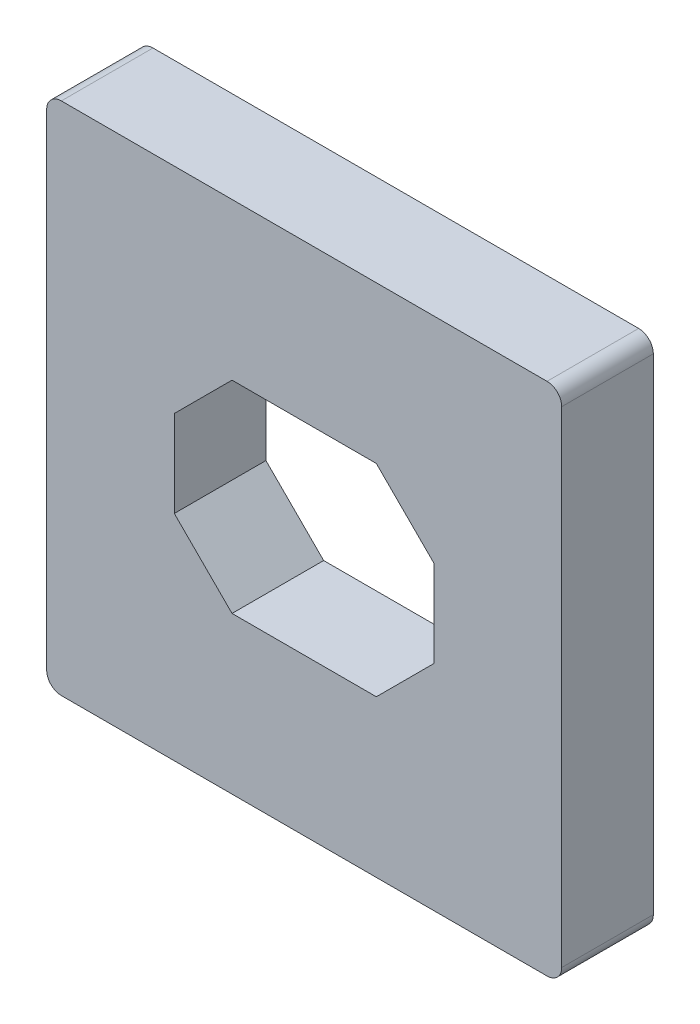
SolidWorks part; units mm, degrees
material "PET"
ref_plane "Front Plane" through (0, 0, 0) normal (0, 0, 1) x (1, 0, 0)
ref_plane "Top Plane" through (0, 0, 0) normal (0, 1, 0) x (1, 0, 0)
ref_plane "Right Plane" through (0, 0, 0) normal (1, 0, 0) x (0, 0, -1)
sketch "Sketch1" plane through (0, 0, 0) normal (0, 0, 1) x (1, 0, 0)
  line L0 (4.207, 4.715) -> (-4.207, 4.715) construction
  line L1 (4.715, -4.207) -> (4.715, 4.207) construction
  line L2 (-4.207, -4.715) -> (4.207, -4.715) construction
  line L3 (-4.715, 4.207) -> (-4.715, -4.207) construction
  line L4 (4.207, 4.715) -> (-4.207, 4.715) construction
  line L5 (4.715, -4.207) -> (4.715, 4.207) construction
  line L6 (-4.207, -4.715) -> (4.207, -4.715) construction
  line L7 (-4.715, 4.207) -> (-4.715, -4.207) construction
  line L8 (4.207, 4.461) -> (-4.207, 4.461)
  line L9 (-4.461, 4.207) -> (-4.461, -4.207)
  line L10 (-4.207, -4.461) -> (4.207, -4.461)
  line L11 (4.461, -4.207) -> (4.461, 4.207)
  arc A0 (4.715, 4.207) -> (4.207, 4.715) centre (4.207, 4.207) ccw construction
  arc A1 (4.207, -4.715) -> (4.715, -4.207) centre (4.207, -4.207) ccw construction
  arc A2 (-4.715, -4.207) -> (-4.207, -4.715) centre (-4.207, -4.207) ccw construction
  arc A3 (-4.207, 4.715) -> (-4.715, 4.207) centre (-4.207, 4.207) ccw construction
  arc A4 (4.715, 4.207) -> (4.207, 4.715) centre (4.207, 4.207) ccw construction
  arc A5 (4.207, -4.715) -> (4.715, -4.207) centre (4.207, -4.207) ccw construction
  arc A6 (-4.715, -4.207) -> (-4.207, -4.715) centre (-4.207, -4.207) ccw construction
  arc A7 (-4.207, 4.715) -> (-4.715, 4.207) centre (-4.207, 4.207) ccw construction
  arc A8 (-4.207, 4.461) -> (-4.461, 4.207) centre (-4.207, 4.207) ccw
  arc A9 (-4.461, -4.207) -> (-4.207, -4.461) centre (-4.207, -4.207) ccw
  arc A10 (4.207, -4.461) -> (4.461, -4.207) centre (4.207, -4.207) ccw
  arc A11 (4.461, 4.207) -> (4.207, 4.461) centre (4.207, 4.207) ccw
  dimension "D1" = 0.254
extrude "Boss-Extrude1" add sketch "Sketch1" along normal blind 1.5875
sketch "Sketch2" plane through (0, 0, 1.5875) normal (0, 0, 1) x (1, 0, 0)
  line L1 (-2.25, 1.75) -> (2.25, 1.75)
  line L2 (-2.25, 1.75) -> (-2.25, -1.75)
  line L3 (-2.25, -1.75) -> (2.25, -1.75)
  line L4 (2.25, 1.75) -> (2.25, -1.75)
  line L5 (-2.25, 1.75) -> (2.25, -1.75) construction
  line L6 (-2.25, -1.75) -> (2.25, 1.75) construction
  point P0 (0, 0)
  dimension "D1" = 4.5
  dimension "D2" = 3.5
extrude "Cut-Extrude1" cut sketch "Sketch2" against normal through all
chamfer "Chamfer1" distance 1 angle 45 4 edges at (-2.25, -1.75, 0.7937) (2.25, -1.75, 0.7937) (2.25, 1.75, 0.7937) (-2.25, 1.75, 0.7937)
